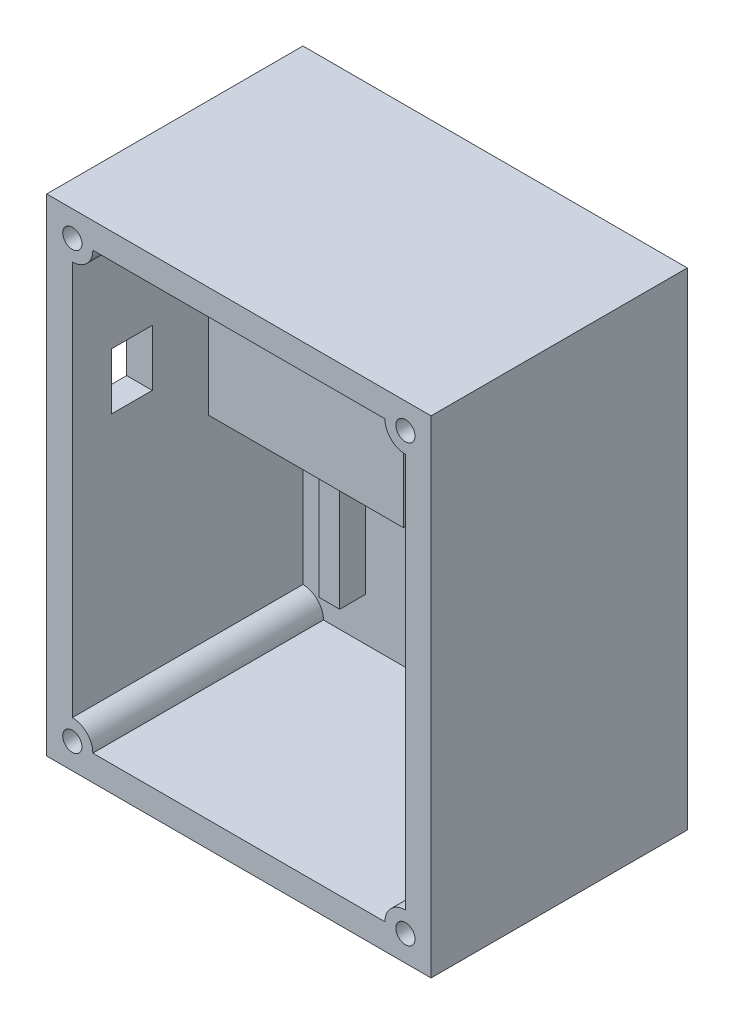
SolidWorks part; units mm, degrees
ref_plane "Front Plane" through (0, 0, 0) normal (0, 0, 1) x (1, 0, 0)
ref_plane "Top Plane" through (0, 0, 0) normal (0, 1, 0) x (1, 0, 0)
ref_plane "Right Plane" through (0, 0, 0) normal (1, 0, 0) x (0, 0, -1)
sketch "Sketch1" plane through (0, 0, 0) normal (0, 0, 1) x (1, 0, 0)
  line L1 (-47.625, -60.325) -> (47.625, -60.325)
  line L2 (-47.625, -60.325) -> (-47.625, 60.325)
  line L3 (-47.625, 60.325) -> (47.625, 60.325)
  line L4 (47.625, -60.325) -> (47.625, 60.325)
  line L5 (-47.625, -60.325) -> (47.625, 60.325) construction
  line L6 (-47.625, 60.325) -> (47.625, -60.325) construction
  point P0 (0, 0)
  dimension "D1" = 95.25
  dimension "D2" = 120.65
extrude "Boss-Extrude1" add sketch "Sketch1" along normal blind 63.5
shell "Shell1" thickness 6.35
ref_plane "Plane1" through (0, 0, 63.5) normal (0, 0, 1) x (1, 0, 0)
sketch "Sketch2" plane through (0, 0, 63.5) normal (0, 0, 1) x (1, 0, 0)
  line L0 (41.275, 53.975) -> (-41.275, 53.975) construction
  line L1 (-41.275, 53.975) -> (-41.275, -53.975) construction
  line L2 (-41.275, 53.975) -> (-36.195, 53.975)
  line L3 (-41.275, 53.975) -> (-41.275, 48.895)
  line L4 (41.275, 53.975) -> (-41.275, 53.975) construction
  line L5 (41.275, -53.975) -> (41.275, 53.975) construction
  line L6 (36.195, 53.975) -> (41.275, 53.975)
  line L7 (41.275, 53.975) -> (41.275, 48.895)
  line L8 (-41.275, -53.975) -> (41.275, -53.975) construction
  line L9 (41.275, -48.895) -> (41.275, -53.975)
  line L10 (41.275, -53.975) -> (36.195, -53.975)
  line L11 (-41.275, -53.975) -> (41.275, -53.975) construction
  line L12 (-41.275, -48.895) -> (-41.275, -53.975)
  line L13 (-41.275, -53.975) -> (-36.195, -53.975)
  arc A0 (-36.195, 53.975) -> (-41.275, 48.895) centre (-41.275, 53.975) cw
  arc A1 (36.195, 53.975) -> (41.275, 48.895) centre (41.275, 53.975) ccw
  arc A2 (41.275, -48.895) -> (36.195, -53.975) centre (41.275, -53.975) ccw
  arc A3 (-41.275, -48.895) -> (-36.195, -53.975) centre (-41.275, -53.975) cw
  dimension "D1" = 5.08
extrude "Boss-Extrude2" add sketch "Sketch2" against normal up to surface (57.15 mm away) up to face at (0, 0, 6.35)
ref_plane "Plane3" through (0, 0, 6.35) normal (0, 0, 1) x (1, 0, 0)
sketch "Sketch5" plane through (0, 0, 6.35) normal (0, 0, 1) x (1, 0, 0)
  line L0 (-36.195, -53.975) -> (36.195, -53.975) construction
  line L5 (11.3665, -26.035) -> (11.3665, -40.6427) construction
  line L6 (11.3665, -26.035) -> (33.655, -26.035)
  line L7 (11.3665, -26.035) -> (11.3665, -20.955)
  line L8 (11.3665, -20.955) -> (33.655, -20.955)
  line L9 (33.655, -26.035) -> (33.655, -20.955)
  line L10 (11.3665, -26.035) -> (33.655, -20.955) construction
  line L11 (11.3665, -20.955) -> (33.655, -26.035) construction
  line L12 (33.655, -26.035) -> (33.655, -28.5697) construction
  line L13 (41.275, -48.895) -> (41.275, 48.895) construction
  circle A0 centre (13.2715, -45.085) radius 1.905
  circle A1 centre (31.75, -45.085) radius 1.905
  point P4 (22.5107, -23.495)
  dimension "D4" = 3.81
  dimension "D3" = 18.4785
  dimension "D1" = 8.89
  dimension "D2" = 19.05
  dimension "D5" = 5.08
  dimension "D6" = 9.525
extrude "Boss-Extrude5" add sketch "Sketch5" along normal blind 6.35
ref_plane "Plane4" through (0, 0, 12.7) normal (0, 0, 1) x (1, 0, 0)
sketch "Sketch7" plane through (0, 0, 12.7) normal (0, 0, 1) x (1, 0, 0)
  circle A0 centre (13.2715, -45.085) radius 1.016
  circle A1 centre (31.75, -45.085) radius 1.016
  dimension "D1" = 2.032
extrude "Boss-Extrude6" add sketch "Sketch7" along normal blind 8.89
ref_plane "Plane5" through (0, 0, 63.5) normal (0, 0, 1) x (1, 0, 0)
sketch "Sketch8" plane through (0, 0, 63.5) normal (0, 0, 1) x (1, 0, 0)
  circle A0 centre (-41.275, 53.975) radius 2.3812
  circle A1 centre (41.275, 53.975) radius 2.3812
  circle A2 centre (41.275, -53.975) radius 2.3812
  circle A3 centre (-41.275, -53.975) radius 2.3812
  arc A4 (-36.195, -53.975) -> (-41.275, -48.895) centre (-41.275, -53.975) ccw construction
  arc A5 (-41.275, 48.895) -> (-36.195, 53.975) centre (-41.275, 53.975) ccw construction
  arc A6 (36.195, 53.975) -> (41.275, 48.895) centre (41.275, 53.975) ccw construction
  arc A7 (41.275, -48.895) -> (36.195, -53.975) centre (41.275, -53.975) ccw construction
  dimension "D1" = 4.7625
extrude "Cut-Extrude1" cut sketch "Sketch8" against normal blind 8.89
ref_plane "Plane7" through (0, 0, 6.35) normal (0, 0, 1) x (1, 0, 0)
sketch "Sketch10" plane through (0, 0, 6.35) normal (0, 0, 1) x (1, 0, 0)
  line L0 (-30.8991, -43.307) -> (-30.8991, -9.7028)
  line L1 (-30.8991, -9.7028) -> (5.0165, -9.7028)
  line L2 (5.0165, -9.7028) -> (5.0165, -43.307)
  line L3 (5.0165, -43.307) -> (-0.0635, -43.307)
  line L4 (-0.0635, -43.307) -> (-0.0635, -14.7828)
  line L5 (-0.0635, -14.7828) -> (-25.8191, -14.7828)
  line L6 (-25.8191, -14.7828) -> (-25.8191, -43.307)
  line L7 (-25.8191, -43.307) -> (-30.8991, -43.307)
  line L8 (-36.195, -53.975) -> (36.195, -53.975) construction
  line L11 (11.3665, -20.955) -> (11.3665, -26.035) construction
  dimension "D1" = 5.08
  dimension "D2" = 25.7556
  dimension "D3" = 28.5242
  dimension "D4" = 5.08
  dimension "D5" = 10.668
  dimension "D6" = 6.35
extrude "Boss-Extrude7" add sketch "Sketch10" along normal blind 6.35
ref_plane "Plane8" through (-47.625, 0, 0) normal (-1, 0, 0) x (0, 0, 1)
sketch "Sketch13" plane through (-47.625, 0, 0) normal (-1, 0, 0) x (0, 0, 1)
  line L0 (0, 60.325) -> (0, -60.325) construction
  line L1 (43.688, 25.4) -> (53.848, 25.4)
  line L2 (43.688, 25.4) -> (43.688, 11.43)
  line L3 (43.688, 11.43) -> (53.848, 11.43)
  line L4 (53.848, 25.4) -> (53.848, 11.43)
  line L5 (43.688, 25.4) -> (53.848, 11.43) construction
  line L6 (43.688, 11.43) -> (53.848, 25.4) construction
  line L10 (63.5, 60.325) -> (0, 60.325) construction
  point P0 (48.768, 18.415)
  dimension "D1" = 13.97
  dimension "D2" = 10.16
  dimension "D3" = 41.91
  dimension "D4" = 48.768
extrude "Cut-Extrude3" cut sketch "Sketch13" against normal up to next
ref_plane "Plane9" through (0, 0, 6.35) normal (0, 0, 1) x (1, 0, 0)
sketch "Sketch15" plane through (0, 0, 6.35) normal (0, 0, 1) x (1, 0, 0)
  line L0 (-31.75, 53.975) -> (-31.75, 46.355)
  line L1 (36.195, 53.975) -> (-36.195, 53.975) construction
  line L2 (-31.75, 46.355) -> (31.75, 46.355)
  line L3 (31.75, 46.355) -> (31.75, 53.975)
  line L4 (36.195, 53.975) -> (-36.195, 53.975) construction
  line L5 (31.75, 53.975) -> (35.56, 53.975)
  line L6 (35.56, 53.975) -> (35.56, 42.545)
  line L7 (35.56, 42.545) -> (-35.56, 42.545)
  line L8 (-35.56, 42.545) -> (-35.56, 53.975)
  line L10 (-31.75, 53.975) -> (-35.56, 53.975)
  line L11 (-35.56, 53.975) -> (-47.625, 53.975) construction
  line L12 (35.56, 53.975) -> (47.625, 53.975) construction
  line L13 (47.625, -60.325) -> (47.625, 60.325) construction
  line L14 (-47.625, 34.925) -> (-47.625, -34.925) construction
  dimension "D1" = 63.5
  dimension "D2" = 3.81
  dimension "D3" = 3.81
  dimension "D4" = 3.81
  dimension "D5" = 7.62
extrude "Boss-Extrude8" add sketch "Sketch15" along normal blind 31.75
ref_plane "Plane10" through (0, 0, 6.35) normal (0, 0, 1) x (1, 0, 0)
sketch "Sketch16" plane through (0, 0, 6.35) normal (0, 0, 1) x (1, 0, 0)
  line L1 (-39.243, 1.143) -> (9.017, 1.143)
  line L2 (-39.243, 1.143) -> (-39.243, 35.687)
  line L3 (-39.243, 35.687) -> (9.017, 35.687)
  line L4 (9.017, 1.143) -> (9.017, 35.687)
  line L5 (-39.243, 1.143) -> (9.017, 35.687) construction
  line L6 (-39.243, 35.687) -> (9.017, 1.143) construction
  line L7 (36.195, 53.975) -> (-36.195, 53.975) construction
  line L10 (-47.625, 34.925) -> (-47.625, -34.925) construction
  point P0 (-15.113, 18.415)
  dimension "D1" = 48.26
  dimension "D2" = 34.544
  dimension "D3" = 35.56
  dimension "D4" = 32.512
extrude "Boss-Extrude9" add sketch "Sketch16" along normal blind 25.4
